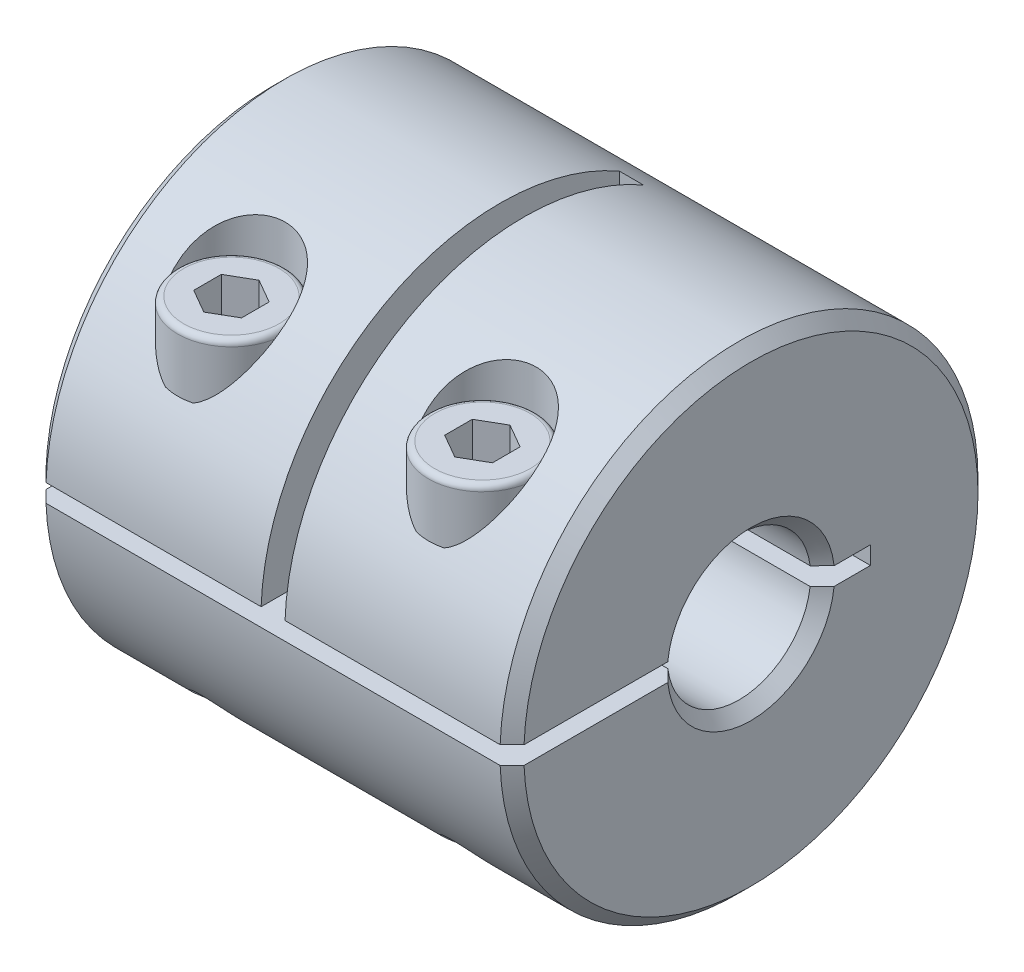
SolidWorks part; units mm, degrees
ref_plane "Front Plane" through (0, 0, 0) normal (0, 0, 1) x (1, 0, 0)
ref_plane "Top Plane" through (0, 0, 0) normal (0, 1, 0) x (1, 0, 0)
ref_plane "Right Plane" through (0, 0, 0) normal (1, 0, 0) x (0, 0, -1)
sketch "Sketch1" plane through (0, 0, 0) normal (1, 0, 0) x (0, 0, -1)
  circle A0 centre (0, 0) radius 10
  dimension "Dim D" = 20
extrude "Boss-Extrude1" add sketch "Sketch1" along normal mid plane 20
sketch "Sketch2" plane through (10, 0, 0) normal (1, 0, 0) x (0, 0, -1)
  circle A0 centre (0, 0) radius 3
  dimension "Dim d2" = 6
extrude "Cut-Extrude1" cut sketch "Sketch2" against normal through all
sketch "Sketch5" plane through (10, 0, 0) normal (1, 0, 0) x (0, 0, -1)
  line L0 (0, 0) -> (5, 0) construction
  line L1 (-9.993, 0.375) -> (5, 0.375)
  line L2 (3, 0.375) -> (3, -0.375) construction
  line L3 (-9.993, -0.375) -> (5, -0.375)
  line L4 (5, 0.375) -> (5, -0.375)
  circle A0 centre (0, 0) radius 10 construction
  arc A1 (-9.993, 0.375) -> (-9.993, -0.375) centre (0, 0) ccw
  circle A2 centre (0, 0) radius 3 construction
  dimension "D1" = 0.75
  dimension "D2" = 2
extrude "Cut-Extrude2" cut sketch "Sketch5" against normal through all
sketch "Sketch6" plane through (0, 0, -5) normal (0, 0, 1) x (1, 0, 0)
  line L0 (-10, -0.375) -> (10, -0.375) construction
  line L1 (-0.5, -0.375) -> (0.5, -0.375)
  line L2 (-0.5, -0.375) -> (-0.5, 10)
  line L3 (-0.5, 10) -> (0.5, 10)
  line L4 (0.5, -0.375) -> (0.5, 10)
  line L5 (10, 10) -> (-10, 10) construction
  line L6 (0, 0) -> (0, 10) construction
  line L7 (10, -10) -> (10, 10) construction
  dimension "Dim L2" = 9.5
extrude "Cut-Extrude3" cut sketch "Sketch6" along normal through all
sketch "Sketch7" plane through (0, -0.375, 0) normal (0, 1, 0) x (1, 0, 0)
  line L0 (5.25, -2.9765) -> (5.25, -9.993) construction
  line L1 (10, -2.9765) -> (0.5, -2.9765) construction
  line L2 (0.5, -9.993) -> (10, -9.993) construction
  line L3 (10, -9.993) -> (10, 10) construction
  circle A0 centre (5.25, -6.4847) radius 1.25
  dimension "Dim M" = 2.5
  dimension "Dim L1" = 4.75
extrude "Cut-Extrude4" cut sketch "Sketch7" against normal through all and the other way through all
ref_plane "Plane1" through (0, 10, 0) normal (0, 1, 0) x (-1, 0, 0)
ref_plane "Plane2" through (0, 5, 0) normal (0, 1, 0) x (-1, 0, 0)
sketch "Sketch8" plane through (0, 5, 0) normal (0, 1, 0) x (-1, 0, 0)
  circle A0 centre (-5.25, 6.4847) radius 2.25
  dimension "Dim bolt diameter" = 4.5
extrude "Cut-Extrude5" cut sketch "Sketch8" along normal through all
mirror "Mirror1" about plane through (0, 0, 0) normal (1, 0, 0) of "Cut-Extrude5", "Cut-Extrude4"
ref_plane "Plane4" through (0, -10, 0) normal (0, -1, 0) x (1, 0, 0)
ref_plane "Plane5" through (0, -5, 0) normal (0, -1, 0) x (1, 0, 0)
sketch "Sketch9" plane through (0, 5, 0) normal (0, 1, 0) x (1, 0, 0)
  circle A0 centre (5.25, -6.4847) radius 2.25
  circle A1 centre (5.25, -6.4847) radius 2.25 construction
extrude "Boss-Extrude2" add sketch "Sketch9" along normal blind 2.5 separate body
sketch "Sketch10" plane through (0, 7.5, 0) normal (0, 1, 0) x (1, 0, 0)
  circle A0 centre (5.25, -6.4847) radius 1.25 construction
  circle A1 centre (5.25, -6.4847) radius 1.25
extrude "Boss-Extrude3" add sketch "Sketch10" against normal up to surface (12.5 mm away) up to plane "Plane5"
fillet "Fillet1" radius 0.25 2 edges at (5.25, -5, 5.2347) (5.25, 7.5, 8.7347)
sketch "Sketch11" plane through (0, 7.5, 0) normal (0, 1, 0) x (1, 0, 0)
  line L1 (5.25, -5.33) -> (4.25, -5.9074)
  line L2 (4.25, -5.9074) -> (4.25, -7.0621)
  line L3 (4.25, -7.0621) -> (5.25, -7.6394)
  line L4 (5.25, -7.6394) -> (6.25, -7.0621)
  line L5 (6.25, -7.0621) -> (6.25, -5.9074)
  line L6 (6.25, -5.9074) -> (5.25, -5.33)
  circle A0 centre (5.25, -6.4847) radius 1 construction
  dimension "Dim hex width" = 2
extrude "Cut-Extrude6" cut sketch "Sketch11" against normal blind 2
mirror "Mirror2" about plane through (0, 0, 0) normal (1, 0, 0) of bodies 111
chamfer "Chamfer1" distance 0.5 angle 45 6 edges at (-10, 0, -10) (10, 0, -10) (-10, 3, 0) (-10, -3, 0) (10, -3, 0) (10, 3, 0)
